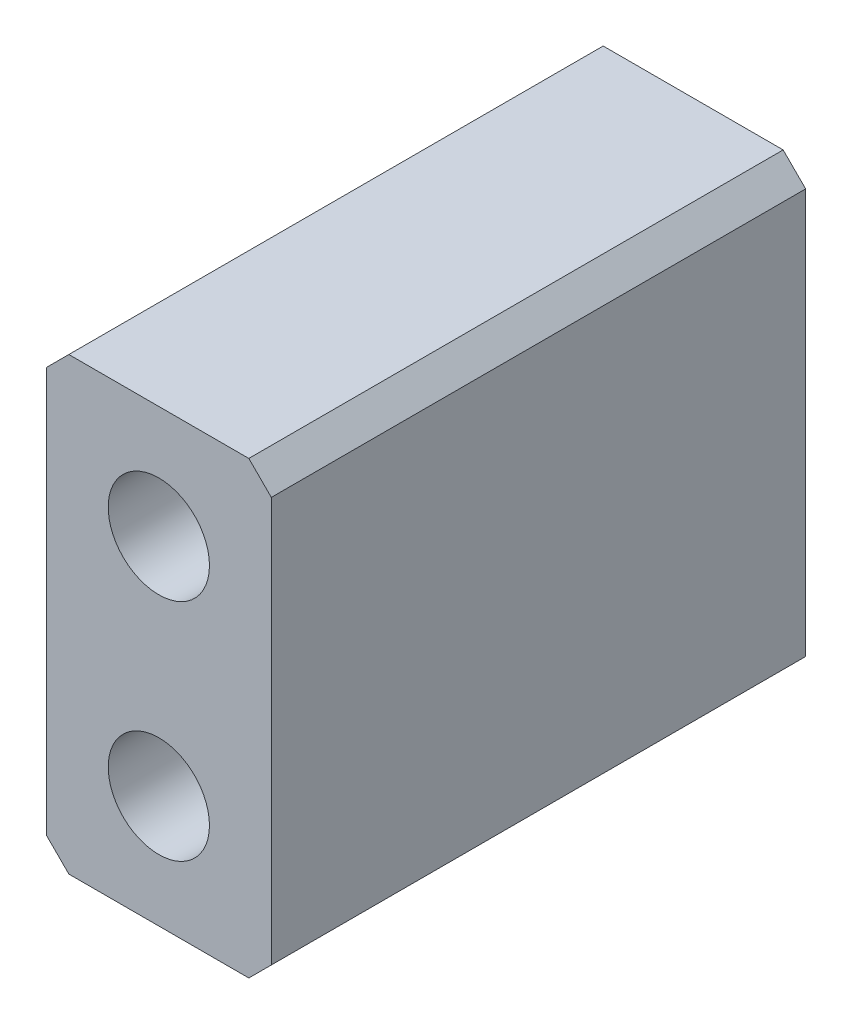
SolidWorks part; units mm, degrees
material "ABS"
ref_plane "前视基准面" through (0, 0, 0) normal (0, 0, 1) x (1, 0, 0)
ref_plane "上视基准面" through (0, 0, 0) normal (0, 1, 0) x (1, 0, 0)
ref_plane "右视基准面" through (0, 0, 0) normal (1, 0, 0) x (0, 0, -1)
sketch "草图1" plane through (0, 0, 0) normal (0, 0, 1) x (1, 0, 0)
  line L0 (0, 0) -> (0, 10) construction
  line L1 (-10, 20) -> (10, 20)
  line L2 (-10, 20) -> (-10, -20)
  line L3 (-10, -20) -> (10, -20)
  line L4 (10, 20) -> (10, -20)
  line L5 (-10, 20) -> (10, -20) construction
  line L6 (-10, -20) -> (10, 20) construction
  line L7 (0, 0) -> (0, -10) construction
  circle A0 centre (0, 10) radius 4.5
  circle A1 centre (0, -10) radius 4.5
  point P0 (0, 0)
extrude "凸台-拉伸1" add sketch "草图1" along normal blind 47.5
chamfer "倒角1" distance 2 angle 45 2 edges at (-10, -20, 23.75) (0, -20, 47.5)
chamfer "倒角2" distance 2 angle 45 3 edges at (10, -20, 23.75) (-10, 20, 23.75) (10, 20, 23.75)
